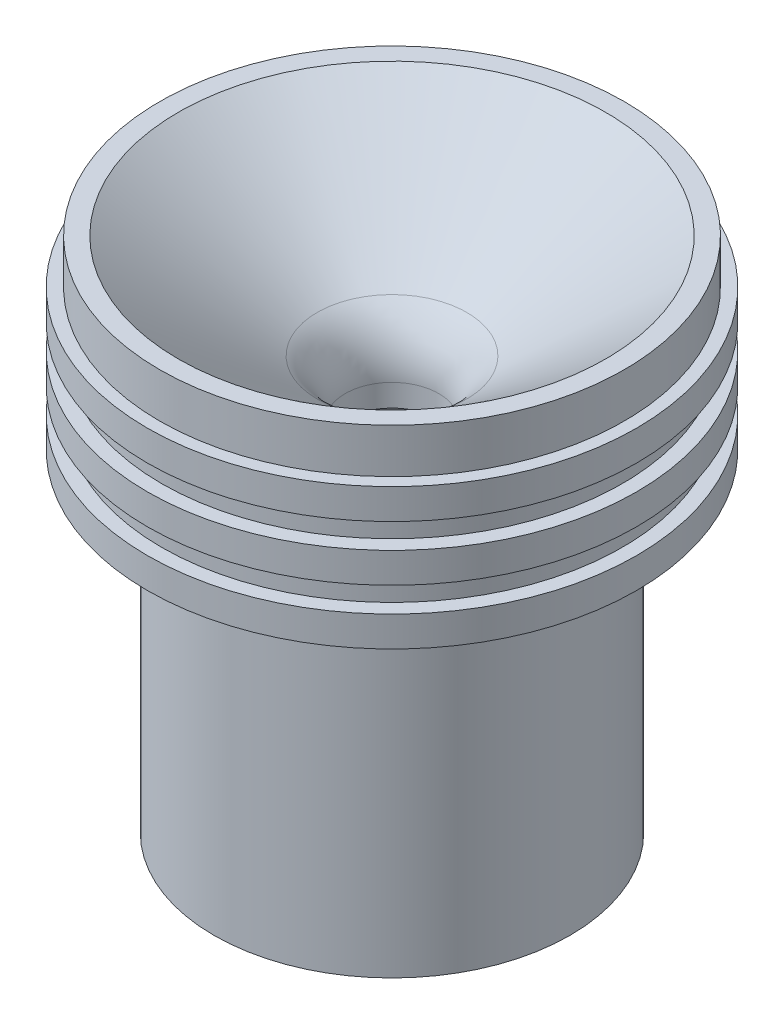
SolidWorks part; units mm, degrees
material "C (Graphite)"
ref_plane "Front Plane" through (0, 0, 0) normal (0, 0, 1) x (1, 0, 0)
ref_plane "Top Plane" through (0, 0, 0) normal (0, 1, 0) x (1, 0, 0)
ref_plane "Right Plane" through (0, 0, 0) normal (1, 0, 0) x (0, 0, -1)
sketch "Sketch1" plane through (0, 0, 0) normal (0, 0, 1) x (1, 0, 0)
  line L0 (0, 0) -> (-6.6802, 0) construction
  line L1 (-6.6802, 0) -> (-6.6802, -3.175)
  line L2 (-6.6802, -3.175) -> (-21.2795, -50.9273)
  line L3 (0, 0) -> (0, -22.3007) construction
  line L4 (-10.6911, 8.0183) -> (-30.494, 22.8597)
  line L5 (-30.494, 22.8597) -> (-33.1466, 22.8597)
  line L6 (-33.1466, 22.8597) -> (-33.1466, 16.5097)
  line L7 (-33.1466, 16.5097) -> (-34.8992, 16.5097)
  line L8 (-34.8992, 16.5097) -> (-34.8992, 12.1917)
  line L9 (-34.8992, 12.1917) -> (-32.8672, 12.1917)
  line L10 (-32.8672, 12.1917) -> (-32.8672, 8.6357)
  line L11 (-32.8672, 8.6357) -> (-34.8992, 8.6357)
  line L12 (-34.8992, 8.6357) -> (-34.8992, 4.3177)
  line L13 (-34.8992, 4.3177) -> (-32.8672, 4.3177)
  line L14 (-32.8672, 4.3177) -> (-32.8672, 0.7617)
  line L15 (-32.8672, 0.7617) -> (-34.8992, 0.7617)
  line L16 (-34.8992, 0.7617) -> (-34.8992, -3.5563)
  line L17 (-34.8992, -3.5563) -> (-25.3996, -3.5563)
  line L18 (-25.3996, -3.5563) -> (-25.3996, -50.9273)
  line L19 (-25.3996, -50.9273) -> (-21.2795, -50.9273)
  arc A0 (-6.6802, 0) -> (-10.6911, 8.0183) centre (-16.7005, 0) ccw
  dimension "D5" = 10.0203
  dimension "D1" = 6.6802
  dimension "D2" = 3.175
  dimension "D3" = 17
  dimension "D4" = 47.371
  dimension "D6" = 53.15
  dimension "D7" = 30.494
  dimension "D8" = 2.6527
  dimension "D9" = 1.7526
  dimension "D10" = 6.35
  dimension "D11" = 4.318
  dimension "D12" = 4.318
  dimension "D13" = 3.556
  dimension "D14" = 3.556
  dimension "D15" = 2.032
  dimension "D16" = 4.318
  dimension "D17" = 9.4996
revolve "Revolve1" add sketch "Sketch1" angle 360 about L3
